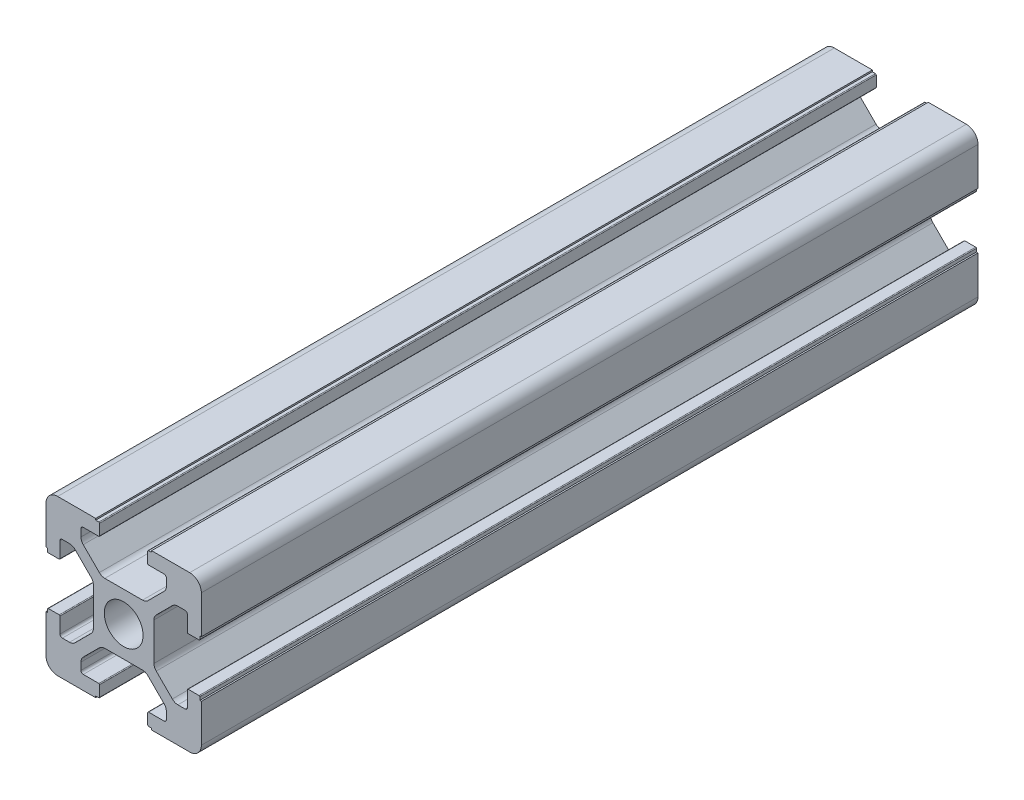
SolidWorks part; units mm, degrees
material "6063-T5"
ref_plane "前视基准面" through (0, 0, 0) normal (0, 0, 1) x (1, 0, 0)
ref_plane "上视基准面" through (0, 0, 0) normal (0, 1, 0) x (1, 0, 0)
ref_plane "右视基准面" through (0, 0, 0) normal (1, 0, 0) x (0, 0, -1)
sketch "草图1" plane through (0, 0, 0) normal (0, 0, 1) x (1, 0, 0)
  line L0 (-1.4389, 10) -> (24.3741, 10) construction
  line L1 (20, 13.6) -> (20, 20)
  line L2 (0, 0) -> (0, 6.4)
  line L3 (0, 20) -> (6.4, 20)
  line L4 (20, 0) -> (20, 6.4)
  line L5 (10, 21.5388) -> (10, -2.4017) construction
  line L6 (6.9, 18.3) -> (6.9, 19.7)
  line L7 (6.8, 18.2) -> (4.8, 18.2)
  line L8 (4.5, 17.9) -> (4.5, 16.9749)
  line L9 (4.7929, 16.2678) -> (6.8678, 14.1929)
  line L10 (7.5749, 13.9) -> (12.4251, 13.9)
  line L11 (6.8, 19.8) -> (6.4, 19.8)
  line L12 (6.4, 19.8) -> (6.4, 20)
  line L13 (0, 13.6) -> (0.2, 13.6)
  line L14 (0.2, 13.6) -> (0.2, 13.2)
  line L15 (0.3, 13.1) -> (1.7, 13.1)
  line L16 (1.8, 13.2) -> (1.8, 15.2)
  line L17 (2.1, 15.5) -> (3.0251, 15.5)
  line L18 (3.7322, 15.2071) -> (5.8071, 13.1322)
  line L19 (6.1, 12.4251) -> (6.1, 7.5749)
  line L20 (13.6, 19.8) -> (13.6, 20)
  line L21 (13.2, 19.8) -> (13.6, 19.8)
  line L22 (13.1, 18.3) -> (13.1, 19.7)
  line L23 (13.2, 18.2) -> (15.2, 18.2)
  line L24 (15.5, 17.9) -> (15.5, 16.9749)
  line L25 (15.2071, 16.2678) -> (13.1322, 14.1929)
  line L26 (0, 6.4) -> (0.2, 6.4)
  line L27 (0.2, 6.4) -> (0.2, 6.8)
  line L28 (0.3, 6.9) -> (1.7, 6.9)
  line L29 (1.8, 6.8) -> (1.8, 4.8)
  line L30 (2.1, 4.5) -> (3.0251, 4.5)
  line L31 (3.7322, 4.7929) -> (5.8071, 6.8678)
  line L32 (13.6, 20) -> (20, 20)
  line L33 (0, 13.6) -> (0, 20)
  line L34 (13.6, 0.2) -> (13.6, 0)
  line L35 (13.2, 0.2) -> (13.6, 0.2)
  line L36 (13.1, 1.7) -> (13.1, 0.3)
  line L37 (13.2, 1.8) -> (15.2, 1.8)
  line L38 (15.5, 2.1) -> (15.5, 3.0251)
  line L39 (15.2071, 3.7322) -> (13.1322, 5.8071)
  line L40 (4.5, 2.1) -> (4.5, 3.0251)
  line L41 (6.8, 1.8) -> (4.8, 1.8)
  line L42 (6.4, 0.2) -> (6.4, 0)
  line L43 (6.8, 0.2) -> (6.4, 0.2)
  line L44 (6.9, 1.7) -> (6.9, 0.3)
  line L45 (4.7929, 3.7322) -> (6.8678, 5.8071)
  line L46 (7.5749, 6.1) -> (12.4251, 6.1)
  line L47 (20, 6.4) -> (19.8, 6.4)
  line L48 (19.8, 6.4) -> (19.8, 6.8)
  line L49 (19.7, 6.9) -> (18.3, 6.9)
  line L50 (18.2, 6.8) -> (18.2, 4.8)
  line L51 (17.9, 4.5) -> (16.9749, 4.5)
  line L52 (16.2678, 4.7929) -> (14.1929, 6.8678)
  line L53 (13.9, 12.4251) -> (13.9, 7.5749)
  line L54 (16.2678, 15.2071) -> (14.1929, 13.1322)
  line L55 (17.9, 15.5) -> (16.9749, 15.5)
  line L56 (18.2, 13.2) -> (18.2, 15.2)
  line L57 (19.7, 13.1) -> (18.3, 13.1)
  line L58 (19.8, 13.6) -> (19.8, 13.2)
  line L59 (20, 13.6) -> (19.8, 13.6)
  line L60 (0, 0) -> (6.4, 0)
  line L61 (13.6, 0) -> (20, 0)
  arc A0 (6.1, 12.4251) -> (5.8071, 13.1322) centre (5.1, 12.4251) ccw
  arc A1 (7.5749, 13.9) -> (6.8678, 14.1929) centre (7.5749, 14.9) cw
  arc A2 (4.5, 16.9749) -> (4.7929, 16.2678) centre (5.5, 16.9749) ccw
  arc A3 (3.7322, 15.2071) -> (3.0251, 15.5) centre (3.0251, 14.5) ccw
  arc A4 (4.5, 17.9) -> (4.8, 18.2) centre (4.8, 17.9) cw
  arc A5 (1.8, 15.2) -> (2.1, 15.5) centre (2.1, 15.2) cw
  arc A6 (0.3, 13.1) -> (0.2, 13.2) centre (0.3, 13.2) cw
  arc A7 (6.9, 19.7) -> (6.8, 19.8) centre (6.8, 19.7) ccw
  arc A8 (1.7, 13.1) -> (1.8, 13.2) centre (1.7, 13.2) ccw
  arc A9 (6.9, 18.3) -> (6.8, 18.2) centre (6.8, 18.3) cw
  arc A10 (13.1, 19.7) -> (13.2, 19.8) centre (13.2, 19.7) cw
  arc A11 (13.1, 18.3) -> (13.2, 18.2) centre (13.2, 18.3) ccw
  arc A12 (15.5, 17.9) -> (15.2, 18.2) centre (15.2, 17.9) ccw
  arc A13 (15.5, 16.9749) -> (15.2071, 16.2678) centre (14.5, 16.9749) cw
  arc A14 (12.4251, 13.9) -> (13.1322, 14.1929) centre (12.4251, 14.9) ccw
  arc A15 (0.3, 6.9) -> (0.2, 6.8) centre (0.3, 6.8) ccw
  arc A16 (1.7, 6.9) -> (1.8, 6.8) centre (1.7, 6.8) cw
  arc A17 (1.8, 4.8) -> (2.1, 4.5) centre (2.1, 4.8) ccw
  arc A18 (3.7322, 4.7929) -> (3.0251, 4.5) centre (3.0251, 5.5) cw
  arc A19 (6.1, 7.5749) -> (5.8071, 6.8678) centre (5.1, 7.5749) cw
  arc A20 (13.1, 0.3) -> (13.2, 0.2) centre (13.2, 0.3) ccw
  arc A21 (13.1, 1.7) -> (13.2, 1.8) centre (13.2, 1.7) cw
  arc A22 (15.5, 2.1) -> (15.2, 1.8) centre (15.2, 2.1) cw
  arc A23 (15.5, 3.0251) -> (15.2071, 3.7322) centre (14.5, 3.0251) ccw
  arc A24 (12.4251, 6.1) -> (13.1322, 5.8071) centre (12.4251, 5.1) cw
  arc A25 (4.5, 2.1) -> (4.8, 1.8) centre (4.8, 2.1) ccw
  arc A26 (6.9, 0.3) -> (6.8, 0.2) centre (6.8, 0.3) cw
  arc A27 (6.9, 1.7) -> (6.8, 1.8) centre (6.8, 1.7) ccw
  arc A28 (4.5, 3.0251) -> (4.7929, 3.7322) centre (5.5, 3.0251) cw
  arc A29 (7.5749, 6.1) -> (6.8678, 5.8071) centre (7.5749, 5.1) ccw
  arc A30 (19.7, 6.9) -> (19.8, 6.8) centre (19.7, 6.8) cw
  arc A31 (18.3, 6.9) -> (18.2, 6.8) centre (18.3, 6.8) ccw
  arc A32 (18.2, 4.8) -> (17.9, 4.5) centre (17.9, 4.8) cw
  arc A33 (16.2678, 4.7929) -> (16.9749, 4.5) centre (16.9749, 5.5) ccw
  arc A34 (13.9, 7.5749) -> (14.1929, 6.8678) centre (14.9, 7.5749) ccw
  arc A35 (13.9, 12.4251) -> (14.1929, 13.1322) centre (14.9, 12.4251) cw
  arc A36 (16.2678, 15.2071) -> (16.9749, 15.5) centre (16.9749, 14.5) cw
  arc A37 (18.2, 15.2) -> (17.9, 15.5) centre (17.9, 15.2) ccw
  arc A38 (18.3, 13.1) -> (18.2, 13.2) centre (18.3, 13.2) cw
  arc A39 (19.7, 13.1) -> (19.8, 13.2) centre (19.7, 13.2) ccw
  circle A40 centre (10, 10) radius 2.5
  point P39 (0.2, 13.1)
  point P42 (6.9, 19.8)
  point P45 (1.8, 13.1)
  point P48 (6.9, 18.2)
  point P66 (10, 13.9)
  point P83 (6.1, 10)
  dimension "D19" = 1
  dimension "D20" = 1
  dimension "D21" = 0.3
  dimension "D22" = 0.1
  dimension "D23" = 5
  dimension "D1" = 20
  dimension "D2" = 20
  dimension "D3" = 10
  dimension "D4" = 10
  dimension "D5" = 1.8
  dimension "D6" = 0.5
  dimension "D7" = 1.6
  dimension "D8" = 3.1
  dimension "D9" = 6.1
  dimension "D10" = 5.5
  dimension "D11" = 3.1
  dimension "D12" = 6.1
  dimension "D13" = 5.5
  dimension "D14" = 1.8
  dimension "D15" = 0.5
  dimension "D16" = 1.5
  dimension "D17" = 45
  dimension "D18" = 1.6
extrude "凸台-拉伸1" add sketch "草图1" along normal blind 100
fillet "圆角1" radius 1.5 4 edges at (20, 0, 50) (0, 0, 50) (0, 20, 50) (20, 20, 50)
